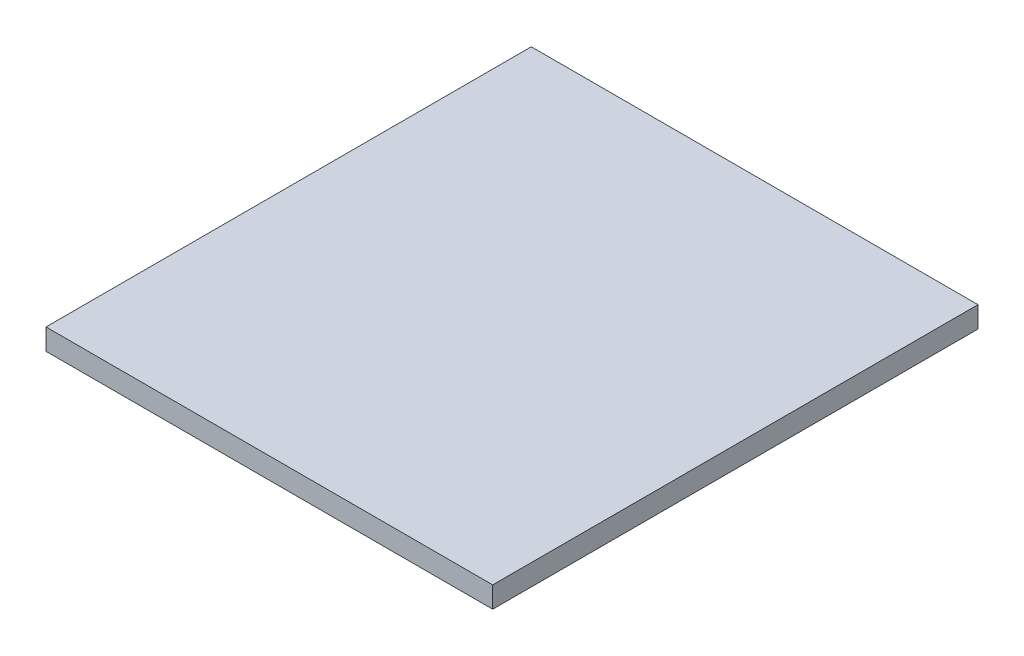
SolidWorks part; units mm, degrees
ref_plane "Front Plane" through (0, 0, 0) normal (0, 0, 1) x (1, 0, 0)
ref_plane "Top Plane" through (0, 0, 0) normal (0, 1, 0) x (1, 0, 0)
ref_plane "Right Plane" through (0, 0, 0) normal (1, 0, 0) x (0, 0, -1)
sketch "Sketch1" plane through (0, 0, 0) normal (0, 1, 0) x (1, 0, 0)
  line L1 (6, 0) -> (94, 0)
  line L2 (6, 0) -> (6, 95.6)
  line L3 (6, 95.6) -> (94, 95.6)
  line L4 (94, 0) -> (94, 95.6)
extrude "Boss-Extrude1" add sketch "Sketch1" along normal blind 4.16
